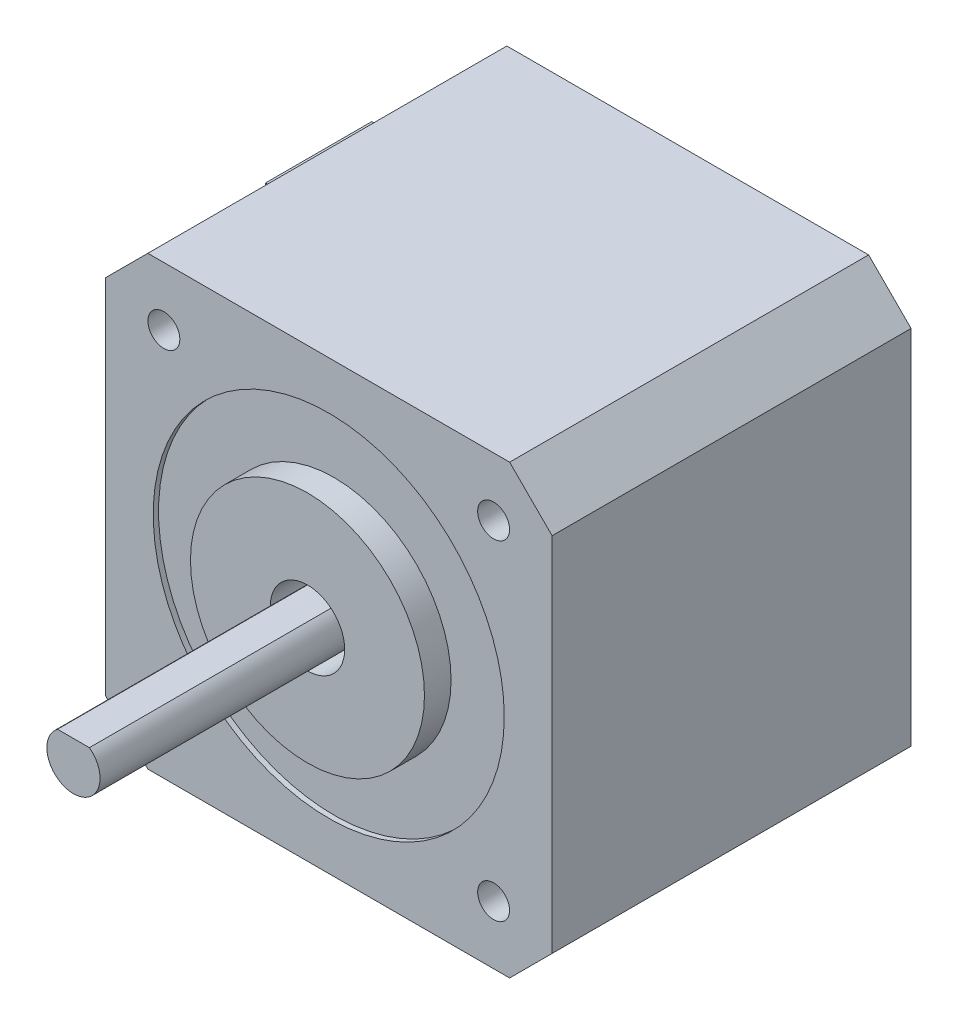
SolidWorks part; units mm, degrees
ref_plane "Front Plane" through (0, 0, 0) normal (0, 0, 1) x (1, 0, 0)
ref_plane "Top Plane" through (0, 0, 0) normal (0, 1, 0) x (1, 0, 0)
ref_plane "Right Plane" through (0, 0, 0) normal (1, 0, 0) x (0, 0, -1)
sketch "Sketch1" plane through (0, 0, 0) normal (0, 0, 1) x (1, 0, 0)
  line L0 (-17.007, 21) -> (-21, 17.007)
  line L1 (-17.007, 21) -> (17.007, 21)
  line L2 (-21, 17.007) -> (-21, -17.007)
  line L3 (-17.007, -21) -> (17.007, -21)
  line L4 (21, 17.007) -> (21, -17.007)
  line L5 (17.007, 21) -> (21, 17.007)
  line L6 (21, -17.007) -> (17.007, -21)
  line L7 (-21, -17.007) -> (-17.007, -21)
  line L8 (-19.0035, 19.0035) -> (19.0035, -19.0035) construction
  line L9 (19.0035, 19.0035) -> (-19.0035, -19.0035) construction
  point P0 (-21, 21)
  point P1 (21, -21)
  point P2 (-21, -21)
  point P3 (21, 21)
  point P16 (0, 0)
  dimension "D1" = 42
  dimension "D2" = 42
  dimension "D3" = 53.75
extrude "Boss-Extrude1" add sketch "Sketch1" along normal blind 33.75
sketch "Sketch2" plane through (0, 0, 33.75) normal (0, 0, 1) x (1, 0, 0)
  line L0 (-21, 17.007) -> (-21, -17.007) construction
  line L1 (17.007, 21) -> (-17.007, 21) construction
  circle A0 centre (0, 0) radius 16.5
  dimension "D1" = 33
  dimension "D2" = 21
  dimension "D3" = 21
extrude "Cut-Extrude1" cut sketch "Sketch2" against normal blind 0.5 contours A0
sketch "Sketch3" plane through (0, 0, 33.25) normal (0, 0, 1) x (1, 0, 0)
  circle A0 centre (0, 0) radius 11
  dimension "D1" = 22
extrude "Boss-Extrude2" add sketch "Sketch3" along normal blind 2.5
sketch "Sketch4" plane through (0, 0, 35.75) normal (0, 0, 1) x (1, 0, 0)
  circle A0 centre (0, 0) radius 3.5
  dimension "D1" = 7
extrude "Cut-Extrude2" cut sketch "Sketch4" against normal blind 5
sketch "Sketch5" plane through (0, 0, 30.75) normal (0, 0, 1) x (1, 0, 0)
  line L0 (-1.5, 2) -> (1.5, 2)
  arc A0 (-1.5, 2) -> (1.5, 2) centre (0, 0) ccw
  dimension "D1" = 5
  dimension "D2" = 3
extrude "Boss-Extrude3" add sketch "Sketch5" along normal blind 27
sketch "Sketch6" plane through (0, 0, 33.75) normal (0, 0, 1) x (1, 0, 0)
  line L1 (-15.5, 15.5) -> (15.5, 15.5) construction
  line L2 (-15.5, 15.5) -> (-15.5, -15.5) construction
  line L3 (-15.5, -15.5) -> (15.5, -15.5) construction
  line L4 (15.5, 15.5) -> (15.5, -15.5) construction
  circle A0 centre (0, 0) radius 21.9203 construction
  circle A1 centre (-15.5, 15.5) radius 1.5
  circle A2 centre (15.5, 15.5) radius 1.5
  circle A3 centre (15.5, -15.5) radius 1.5
  circle A4 centre (-15.5, -15.5) radius 1.5
  dimension "D1" = 31
  dimension "D2" = 3
  dimension "D3" = 3
  dimension "D4" = 3
  dimension "D5" = 3
extrude "Cut-Extrude3" cut sketch "Sketch6" against normal blind 5 contours A4 | A3 | A1 | A2
ref_plane "Plane1" through (0, 0, 16.875) normal (0, 0, -1) x (-1, 0, 0)
mirror "Mirror1" about plane through (0, 0, 16.875) normal (0, 0, -1) of "Cut-Extrude3"
sketch "Sketch7" plane through (-21, 0, 0) normal (-1, 0, 0) x (0, 0, 1)
  line L0 (0, 17.007) -> (0, -17.007) construction
  line L1 (0, 8.5) -> (10, 8.5)
  line L2 (0, 8.5) -> (0, -8.5)
  line L3 (0, -8.5) -> (10, -8.5)
  line L4 (10, 8.5) -> (10, -8.5)
  line L5 (10, 0) -> (0, 0) construction
  dimension "D1" = 17
  dimension "D2" = 10
extrude "Boss-Extrude4" add sketch "Sketch7" along normal blind 8.7
